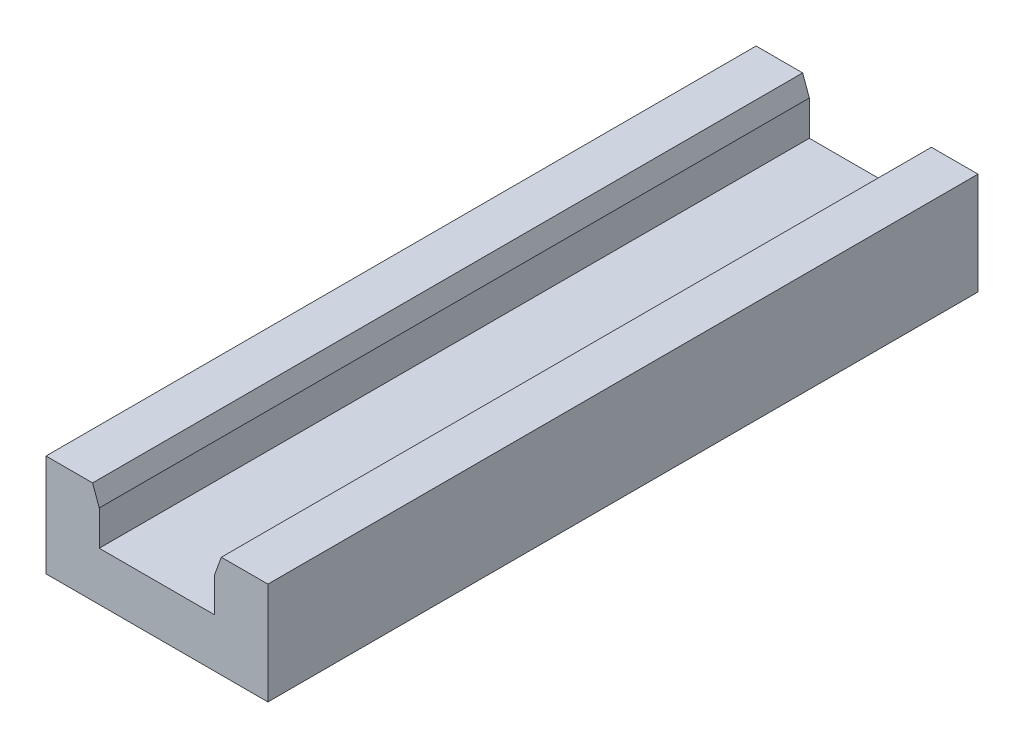
SolidWorks part; units mm, degrees
ref_plane "Plan de face" through (0, 0, 0) normal (0, 0, 1) x (1, 0, 0)
ref_plane "Plan de dessus" through (0, 0, 0) normal (0, 1, 0) x (1, 0, 0)
ref_plane "Plan de droite" through (0, 0, 0) normal (1, 0, 0) x (0, 0, -1)
sketch "Esquisse1" plane through (0, 0, 0) normal (0, 0, 1) x (1, 0, 0)
  line L0 (38, 19) -> (12, 19)
  line L1 (50, 8) -> (50, 31)
  line L2 (39.5068, 31) -> (50, 31)
  line L3 (0, 31) -> (0, 8)
  line L5 (0, 8) -> (50, 8)
  line L6 (38, 19) -> (38, 26.8601)
  line L7 (12, 26.8601) -> (10.4932, 31)
  line L8 (38, 26.8601) -> (39.5068, 31)
  line L12 (10.4932, 31) -> (0, 31)
  line L14 (12, 19) -> (12, 26.8601)
extrude "Extrusion1" add sketch "Esquisse1" along normal blind 160
